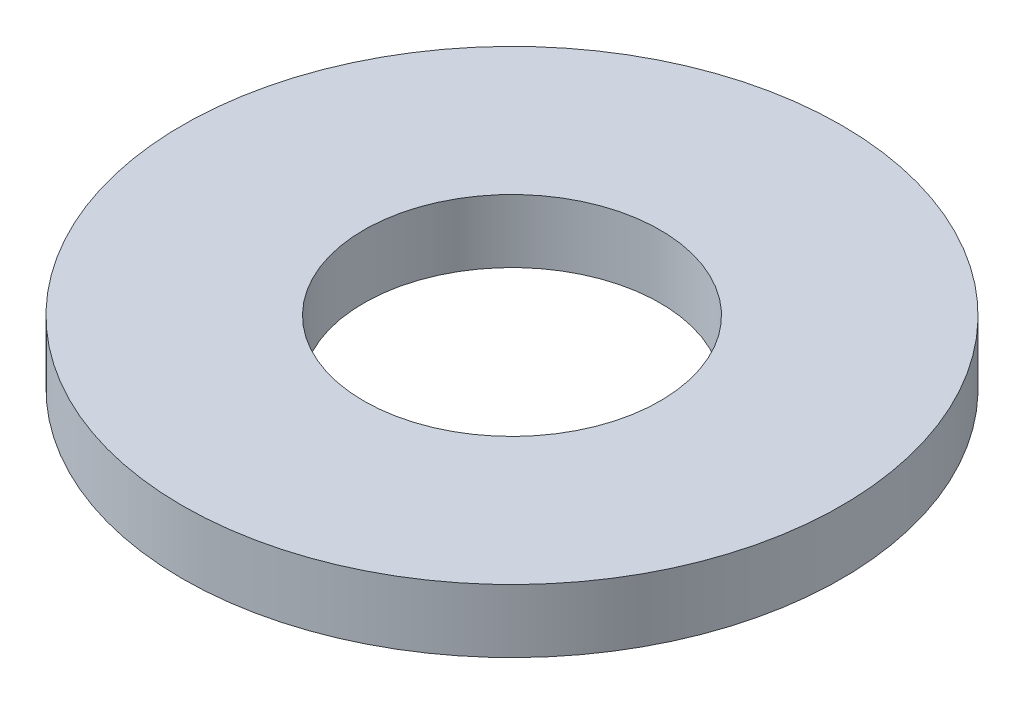
SolidWorks part; units mm, degrees
ref_plane "Front Plane" through (0, 0, 0) normal (0, 0, 1) x (1, 0, 0)
ref_plane "Top Plane" through (0, 0, 0) normal (0, 1, 0) x (1, 0, 0)
ref_plane "Right Plane" through (0, 0, 0) normal (1, 0, 0) x (0, 0, -1)
sketch "Sketch1" plane through (0, 0, 0) normal (0, 1, 0) x (1, 0, 0)
  circle A0 centre (0, 0) radius 7.9375
  dimension "OD" = 15.875
extrude "Boss-Extrude1" add sketch "Sketch1" along normal blind 1.524
sketch "Sketch5" plane through (0, 1.524, 0) normal (0, 1, 0) x (-1, 0, 0)
  circle A0 centre (0, 0) radius 3.5687
  dimension "ID" = 7.1374
extrude "Cut-Extrude1" cut sketch "Sketch5" against normal through all
